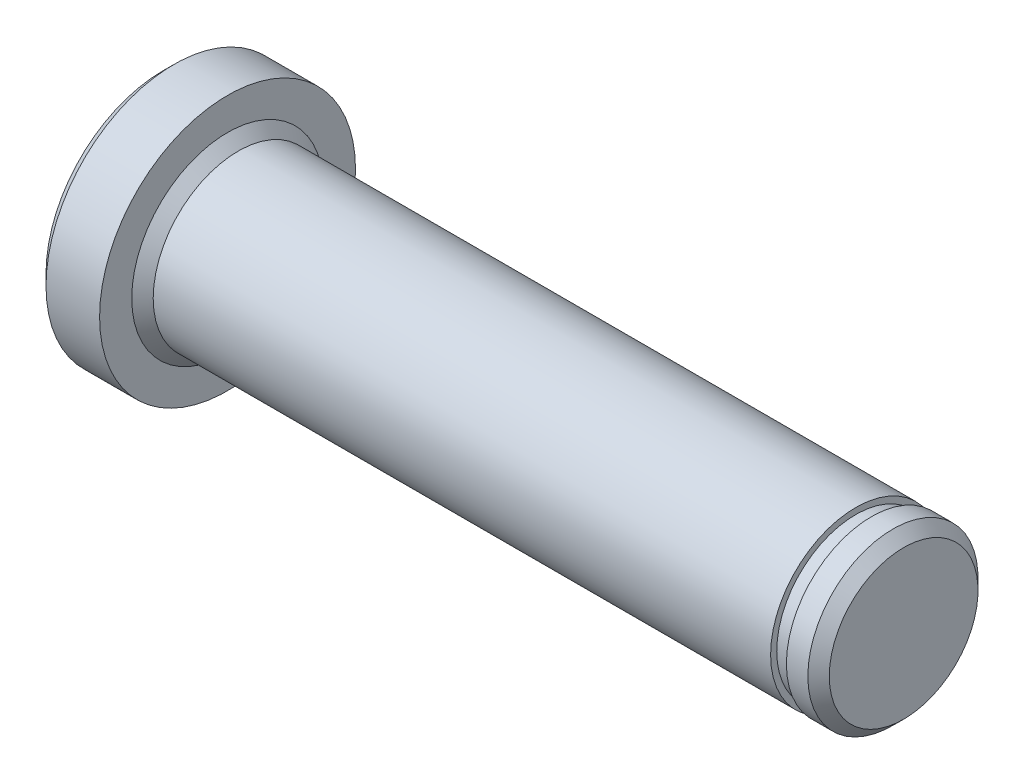
SolidWorks part; units mm, degrees
material "AISI 4340 Steel, normalized"
ref_plane "Front Plane" through (0, 0, 0) normal (0, 0, 1) x (1, 0, 0)
ref_plane "Top Plane" through (0, 0, 0) normal (0, 1, 0) x (1, 0, 0)
ref_plane "Right Plane" through (0, 0, 0) normal (1, 0, 0) x (0, 0, -1)
sketch "Sketch1" plane through (0, 0, 0) normal (0, 0, 1) x (1, 0, 0)
  line L0 (0, 3.9688) -> (0, 5.9688)
  line L1 (0, 5.9688) -> (-3, 5.9688)
  line L2 (-3, 5.9688) -> (-3, 0)
  line L3 (0, 3.9688) -> (29.3, 3.9688)
  line L4 (29.3, 3.9688) -> (29.3, 3.683)
  line L5 (29.3, 3.683) -> (30.0366, 3.683)
  line L6 (30.0366, 3.683) -> (30.0366, 3.9688)
  line L7 (30.0366, 3.9688) -> (31.5366, 3.9688)
  line L8 (31.5366, 3.9688) -> (31.5366, 0)
  line L9 (31.5366, 0) -> (-3, 0)
  line L10 (-20.1991, 0) -> (46.5009, 0) construction
  dimension "D1" = 7.9375
  dimension "D2" = 0.7366
  dimension "D3" = 1.5
  dimension "D4" = 7.366
  dimension "D5" = 3
  dimension "D6" = 2
  dimension "D7" = 29.3
revolve "Revolve1" add sketch "Sketch1" angle 360 about L10
chamfer "Chamfer1" distance 0.5 angle 45 3 edges at (0, 0, 3.9688) (-3, 0, 5.9688) (31.5366, 0, 3.9688)
